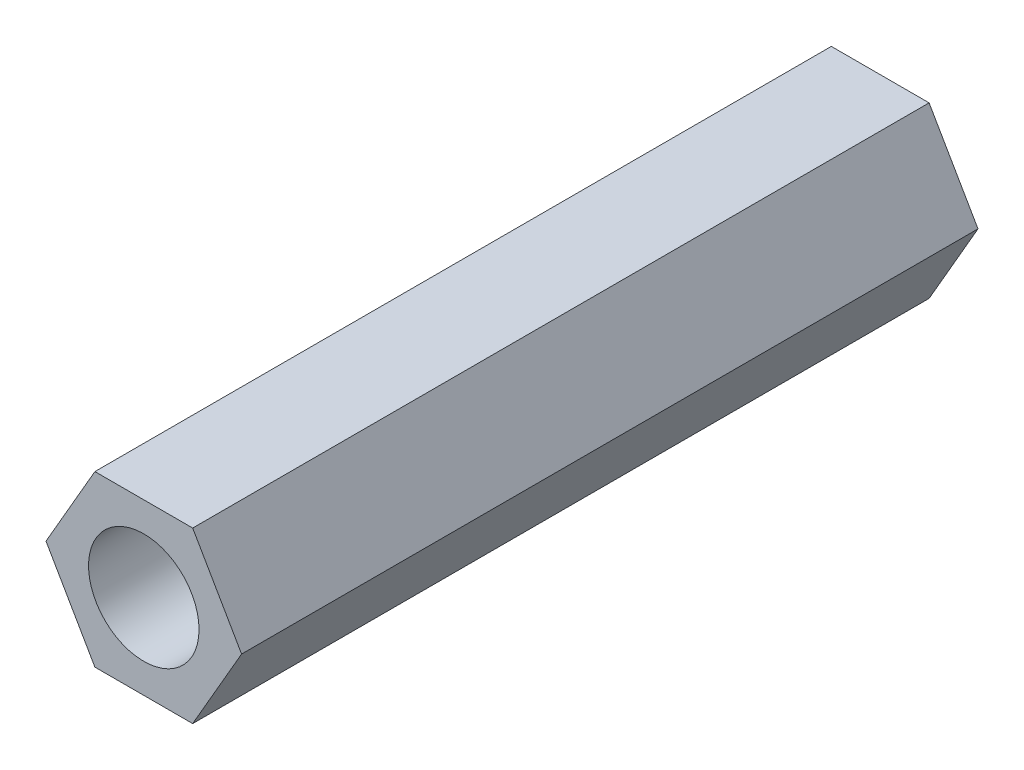
SolidWorks part; units mm, degrees
ref_plane "前视基准面" through (0, 0, 0) normal (0, 0, 1) x (1, 0, 0)
ref_plane "上视基准面" through (0, 0, 0) normal (0, 1, 0) x (1, 0, 0)
ref_plane "右视基准面" through (0, 0, 0) normal (1, 0, 0) x (0, 0, -1)
sketch "草图1" plane through (0, 0, 0) normal (0, 0, 1) x (1, 0, 0)
  line L1 (2.6558, 0) -> (1.3279, 2.3)
  line L2 (1.3279, 2.3) -> (-1.3279, 2.3)
  line L3 (-1.3279, 2.3) -> (-2.6558, 0)
  line L4 (-2.6558, 0) -> (-1.3279, -2.3)
  line L5 (-1.3279, -2.3) -> (1.3279, -2.3)
  line L6 (1.3279, -2.3) -> (2.6558, 0)
  circle A0 centre (0, 0) radius 1.5
  circle A1 centre (0, 0) radius 2.3 construction
  dimension "D1" = 3
  dimension "D2" = 4.6
extrude "凸台-拉伸1" add sketch "草图1" along normal blind 20
